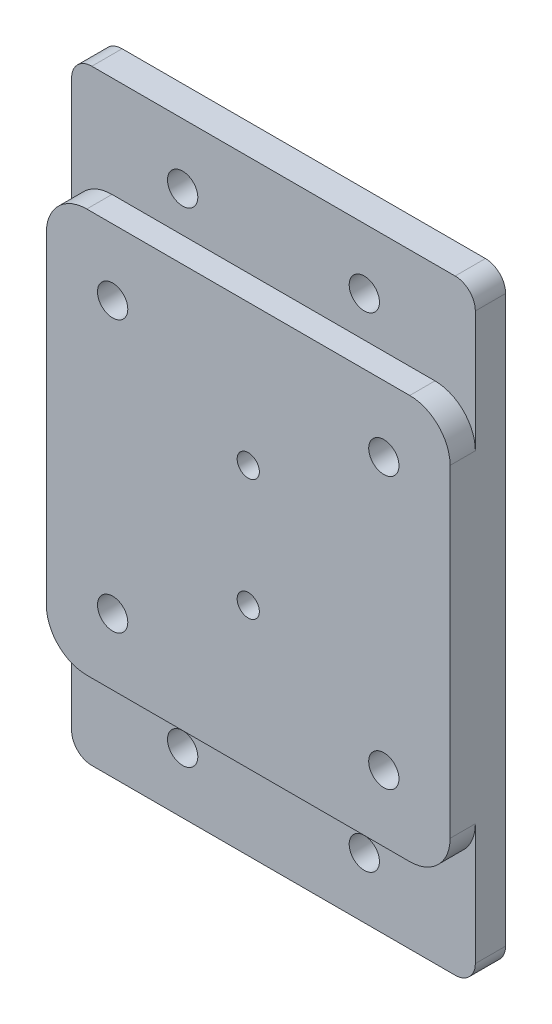
SolidWorks part; units mm, degrees
ref_plane "前视基准面" through (0, 0, 0) normal (0, 0, 1) x (1, 0, 0)
ref_plane "上视基准面" through (0, 0, 0) normal (0, 1, 0) x (1, 0, 0)
ref_plane "右视基准面" through (0, 0, 0) normal (1, 0, 0) x (0, 0, -1)
sketch "草图2" plane through (0, 0, 0) normal (0, 0, 1) x (1, 0, 0)
  line L2 (-25.0628, 26.9355) -> (-65.0628, 26.9355)
  line L3 (-25.0628, 26.9355) -> (-25.0628, -13.0645)
  line L4 (-25.0628, -13.0645) -> (-65.0628, -13.0645)
  line L5 (-65.0628, 26.9355) -> (-65.0628, -13.0645)
extrude "凸台-拉伸1" add sketch "草图2" along normal blind 2.5
sketch "草图5" plane through (0, 0, 0) normal (0, 0, -1) x (-1, 0, 0)
  line L5 (65.0628, 36.9355) -> (25.0628, 36.9355)
  line L6 (65.0628, 36.9355) -> (65.0628, -23.0645)
  line L7 (65.0628, -23.0645) -> (25.0628, -23.0645)
  line L8 (58.0628, 36.9355) -> (32.0628, 36.9355) construction
  line L9 (60.0628, -21.0645) -> (60.0628, 34.9355) construction
  line L10 (32.0628, -23.0645) -> (58.0628, -23.0645) construction
  line L11 (30.0628, 34.9355) -> (30.0628, -21.0645) construction
  line L12 (25.0628, 36.9355) -> (25.0628, -23.0645)
  line L13 (65.0628, 36.9355) -> (25.0628, -23.0645) construction
  line L14 (65.0628, -23.0645) -> (25.0628, 36.9355) construction
  circle A2 centre (36.0628, 30.9355) radius 1.5
  arc A8 (60.0628, 34.9355) -> (58.0628, 36.9355) centre (58.0628, 34.9355) ccw construction
  arc A9 (58.0628, -23.0645) -> (60.0628, -21.0645) centre (58.0628, -21.0645) ccw construction
  arc A10 (30.0628, -21.0645) -> (32.0628, -23.0645) centre (32.0628, -21.0645) ccw construction
  arc A11 (32.0628, 36.9355) -> (30.0628, 34.9355) centre (32.0628, 34.9355) ccw construction
  circle A12 centre (54.0628, 30.9355) radius 1.5
  circle A14 centre (54.0628, -17.0645) radius 1.5
  circle A15 centre (36.0628, -17.0645) radius 1.5
  point P7 (45.0628, 6.9355)
extrude "凸台-拉伸2" add sketch "草图5" along normal blind 3
sketch "草图3" plane through (0, 0, 2.5) normal (0, 0, 1) x (1, 0, 0)
  line L0 (-45.0628, -13.0645) -> (-45.0628, 26.9355) construction
  line L1 (-65.0628, -13.0645) -> (-25.0628, -13.0645) construction
  line L2 (-25.0628, 26.9355) -> (-65.0628, 26.9355) construction
  line L3 (-25.0628, 6.9355) -> (-65.0628, 6.9355) construction
  line L4 (-25.0628, -13.0645) -> (-25.0628, 26.9355) construction
  line L5 (-65.0628, 26.9355) -> (-65.0628, -13.0645) construction
  circle A0 centre (-45.0628, 6.9355) radius 7.4623 construction
sketch "草图4" plane through (0, 0, 2.5) normal (0, 0, 1) x (1, 0, 0)
  circle A4 centre (-31.6278, 20.3706) radius 1.5
  circle A5 centre (-58.4979, 20.3706) radius 1.5
  circle A6 centre (-58.4979, -6.4995) radius 1.5
  circle A7 centre (-31.6278, -6.4995) radius 1.5
  circle A10 centre (-45.0628, 12.9355) radius 1.1
  circle A11 centre (-45.0628, 0.9356) radius 1.1
extrude "切除-拉伸1" cut sketch "草图4" against normal through all
fillet "圆角1" radius 4 4 edges at (-25.0628, 26.9355, 1.25) (-25.0628, -13.0645, 1.25) (-65.0628, -13.0645, 1.25) (-65.0628, 26.9355, 1.25)
fillet "圆角5" radius 2 4 edges at (-25.0628, -23.0645, -1.5) (-65.0628, -23.0645, -1.5) (-65.0628, 36.9355, -1.5) (-25.0628, 36.9355, -1.5)
sketch "草图6" plane through (0, 0, -3) normal (0, 0, -1) x (-1, 0, 0)
  circle A0 centre (58.4979, 20.3706) radius 3
extrude "切除-拉伸2" cut sketch "草图6" against normal blind 3
ref_plane "基准面1" through (0, 6.9355, 0) normal (0, 1, 0) x (1, 0, 0)
ref_plane "基准面2" through (-45.0628, 0, 0) normal (-1, 0, 0) x (0, 0, 1)
mirror "镜向1" about plane through (0, 6.9355, 0) normal (0, 1, 0) of "切除-拉伸2"
mirror "镜向2" about plane through (-45.0628, 0, 0) normal (-1, 0, 0) of "镜向1", "切除-拉伸2"
sketch "草图7" plane through (0, 0, -3) normal (0, 0, -1) x (-1, 0, 0)
  circle A0 centre (45.0628, 12.9355) radius 2
  circle A1 centre (45.0628, 0.9356) radius 2
extrude "切除-拉伸3" cut sketch "草图7" against normal blind 3
